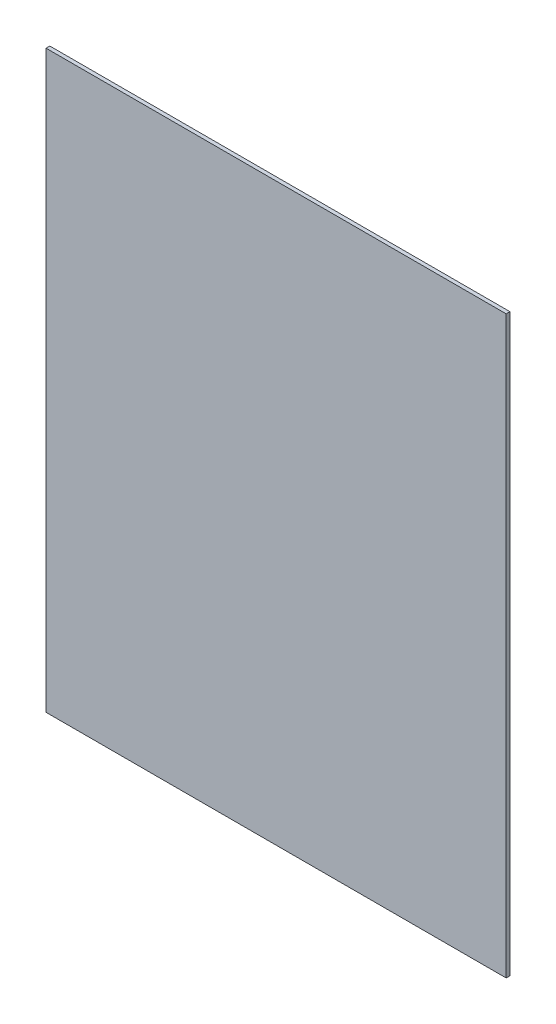
SolidWorks part; units mm, degrees
material "Nylon 101"
ref_plane "Front Plane" through (0, 0, 0) normal (0, 0, 1) x (1, 0, 0)
ref_plane "Top Plane" through (0, 0, 0) normal (0, 1, 0) x (1, 0, 0)
ref_plane "Right Plane" through (0, 0, 0) normal (1, 0, 0) x (0, 0, -1)
sketch "Sketch1" plane through (0, 0, 0) normal (0, 0, 1) x (1, 0, 0)
  line L1 (122, -152.5) -> (-122, -152.5)
  line L2 (122, -152.5) -> (122, 152.5)
  line L3 (122, 152.5) -> (-122, 152.5)
  line L4 (-122, -152.5) -> (-122, 152.5)
  line L5 (122, -152.5) -> (-122, 152.5) construction
  line L6 (122, 152.5) -> (-122, -152.5) construction
  point P0 (0, 0)
  dimension "D1" = 244
  dimension "D2" = 305
extrude "Boss-Extrude1" add sketch "Sketch1" along normal blind 2
